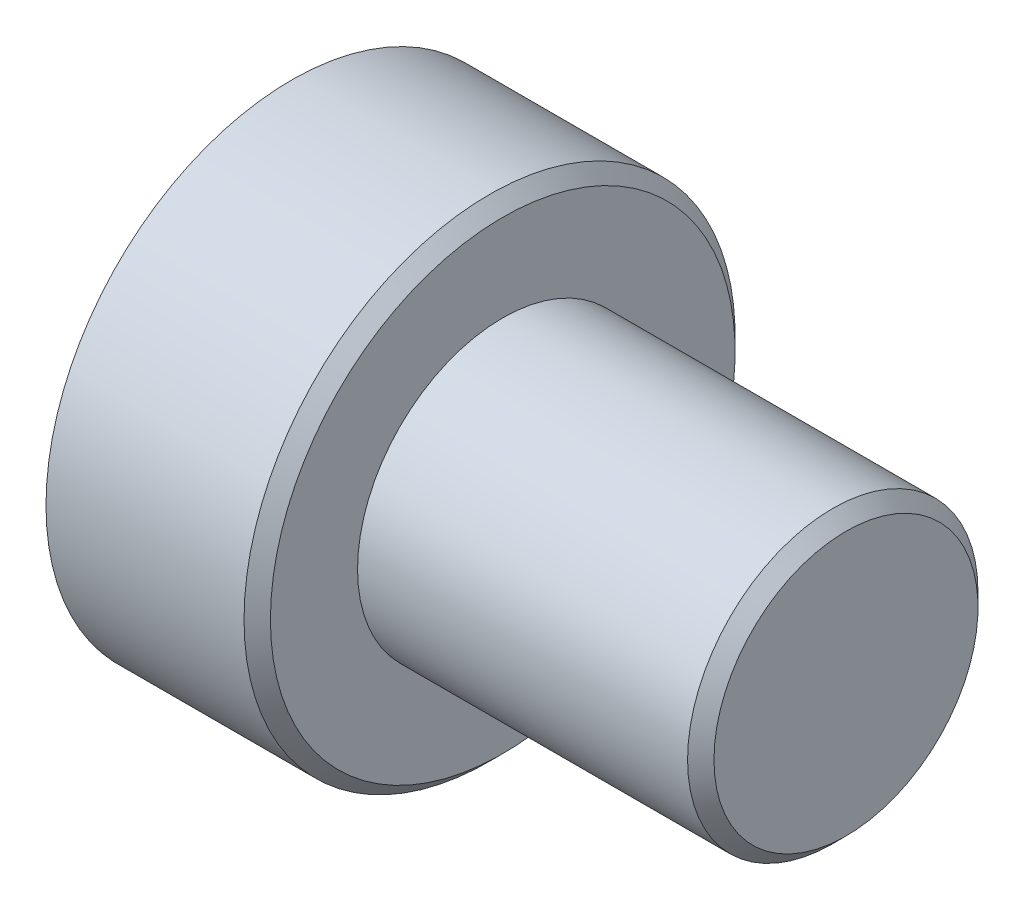
SolidWorks part; units mm, degrees
ref_plane "Front" through (0, 0, 0) normal (0, 0, 1) x (1, 0, 0)
ref_plane "Top" through (0, 0, 0) normal (0, 1, 0) x (1, 0, 0)
ref_plane "Right" through (0, 0, 0) normal (1, 0, 0) x (0, 0, -1)
sketch "Sketch1" plane through (0, 0, 0) normal (0, 0, 1) x (1, 0, 0)
  line L0 (0, 0) -> (18.0386, 0) construction
  line L1 (0, 1.8542) -> (0, 2.3622)
  line L2 (2.032, 1.397) -> (5.334, 1.397)
  line L3 (2.032, 2.3622) -> (2.032, 1.397)
  line L4 (1.905, 0) -> (5.334, 0)
  line L5 (5.334, 1.397) -> (5.334, 0)
  line L6 (0, 2.3622) -> (2.032, 2.3622)
  line L7 (0, 1.8542) -> (1.524, 1.8542)
  line L8 (1.524, 1.8542) -> (1.524, 0.6341)
  line L9 (1.524, 0.6341) -> (1.905, 0)
  dimension "D1" = 2.794
  dimension "D2" = 2.032
  dimension "D3" = 3.302
  dimension "D4" = 4.7244
  dimension "D5" = 1.524
  dimension "D6" = 0.508
  dimension "D7" = 59
  dimension "D8" = 0.381
revolve "Revolve1" add sketch "Sketch1" angle 360 about L0
chamfer "Chamfer1" distance 0.127 angle 45 2 edges at (2.032, 0, 2.3622) (5.334, 0, 1.397)
